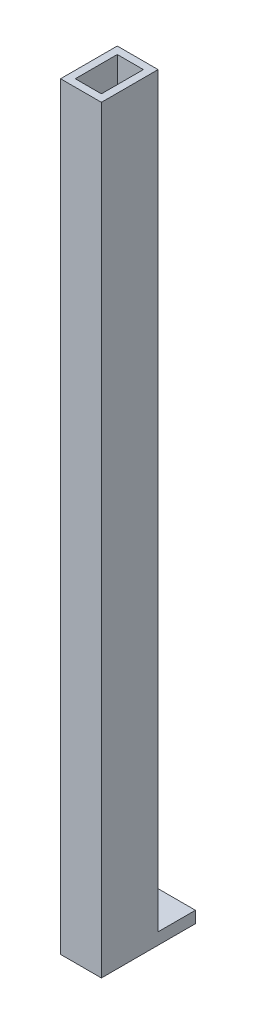
SolidWorks part; units mm, degrees
ref_plane "Front Plane" through (0, 0, 0) normal (0, 0, 1) x (1, 0, 0)
ref_plane "Top Plane" through (0, 0, 0) normal (0, 1, 0) x (1, 0, 0)
ref_plane "Right Plane" through (0, 0, 0) normal (1, 0, 0) x (0, 0, -1)
sketch "Sketch1" plane through (0, 0, 0) normal (0, 1, 0) x (1, 0, 0)
  line L1 (0, 0) -> (11.112, 0)
  line L2 (0, 0) -> (0, 15.43)
  line L3 (0, 15.43) -> (11.112, 15.43)
  line L4 (11.112, 0) -> (11.112, 15.43)
  line L5 (2, 2) -> (9.112, 2)
  line L6 (2, 2) -> (2, 13.43)
  line L7 (2, 13.43) -> (9.112, 13.43)
  line L8 (9.112, 2) -> (9.112, 13.43)
  dimension "D1" = 7.112
  dimension "D2" = 11.43
  dimension "D3" = 2
  dimension "D4" = 2
  dimension "D5" = 2
  dimension "D6" = 2
extrude "Boss-Extrude1" add sketch "Sketch1" along normal blind 203.2
sketch "Sketch2" plane through (0, 0, 0) normal (0, -1, 0) x (1, 0, 0)
  line L0 (0, -15.43) -> (0, 0) construction
  line L1 (0, 0) -> (11.112, 0)
  line L2 (0, 0) -> (0, -25.59)
  line L3 (0, -25.59) -> (11.112, -25.59)
  line L4 (11.112, 0) -> (11.112, -25.59)
  line L5 (11.112, 0) -> (11.112, -15.43) construction
  line L6 (0, 0) -> (11.112, 0) construction
  line L7 (11.112, -15.43) -> (0, -15.43) construction
  line L9 (2, -2) -> (9.112, -2)
  line L10 (2, -2) -> (2, -13.43)
  line L11 (2, -13.43) -> (9.112, -13.43)
  line L12 (9.112, -2) -> (9.112, -13.43)
  dimension "D1" = 0
  dimension "D2" = 0
  dimension "D3" = 0
  dimension "D4" = 10.16
extrude "Boss-Extrude2" add sketch "Sketch2" along normal blind 3.175
